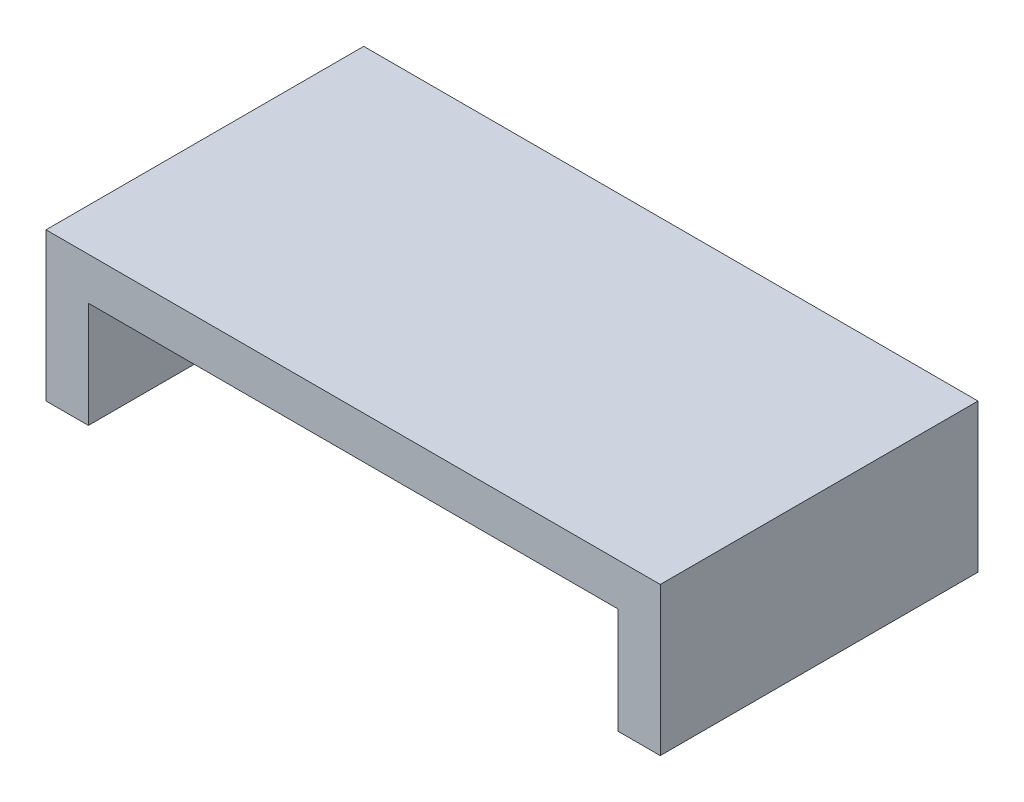
SolidWorks part; units mm, degrees
ref_plane "Front Plane" through (0, 0, 0) normal (0, 0, 1) x (1, 0, 0)
ref_plane "Top Plane" through (0, 0, 0) normal (0, 1, 0) x (1, 0, 0)
ref_plane "Right Plane" through (0, 0, 0) normal (1, 0, 0) x (0, 0, -1)
sketch "Sketch1" plane through (0, 0, 0) normal (0, 0, 1) x (1, 0, 0)
  line L0 (0, 0) -> (0, 70)
  line L2 (0, 70) -> (290, 70)
  line L3 (290, 70) -> (290, 0)
  line L4 (0, 0) -> (20, 0)
  line L5 (20, 0) -> (20, 50)
  line L6 (20, 50) -> (270, 50)
  line L7 (270, 50) -> (270, 0)
  line L8 (270, 0) -> (290, 0)
  dimension "D1" = 250
  dimension "D2" = 50
  dimension "D3" = 20
  dimension "D4" = 20
  dimension "D5" = 20
extrude "Boss-Extrude1" add sketch "Sketch1" along normal blind 150
